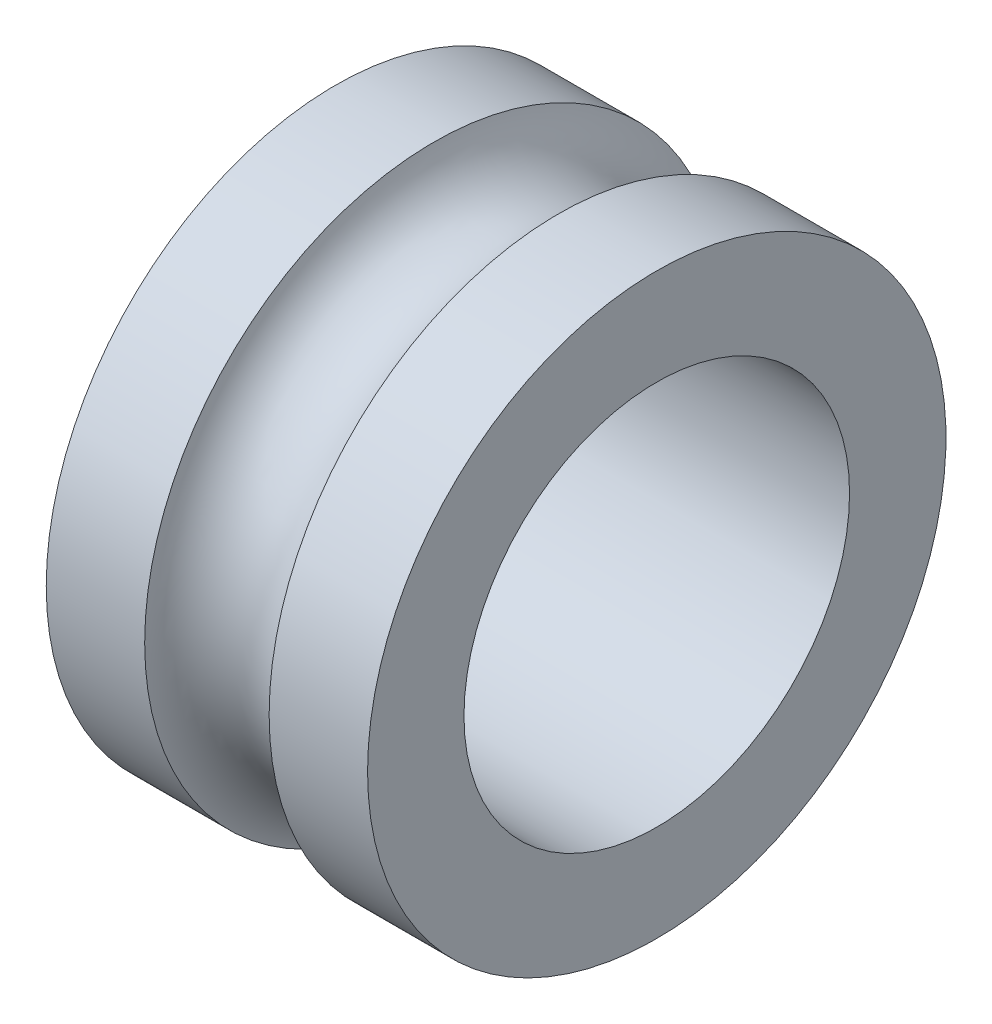
SolidWorks part; units mm, degrees
material "Stainless Steel (ferritic)"
ref_plane "Front Plane" through (0, 0, 0) normal (0, 0, 1) x (1, 0, 0)
ref_plane "Top Plane" through (0, 0, 0) normal (0, 1, 0) x (1, 0, 0)
ref_plane "Right Plane" through (0, 0, 0) normal (1, 0, 0) x (0, 0, -1)
sketch "Sketch1" plane through (0, 0, 0) normal (0, 0, 1) x (1, 0, 0)
  line L0 (-27.4435, -5.7926) -> (-27.4435, -11.7926) construction
  line L1 (-24.9435, -4.2926) -> (-26.4752, -4.2926)
  line L2 (-29.9435, -4.2926) -> (-29.9435, -5.7926)
  line L3 (-29.9435, -5.7926) -> (-24.9435, -5.7926)
  line L4 (-24.9435, -4.2926) -> (-24.9435, -5.7926)
  line L5 (-27.4435, -8.7926) -> (-26.4435, -8.7926) construction
  line L7 (-28.4117, -4.2926) -> (-29.9435, -4.2926)
  arc A0 (-28.4117, -4.2926) -> (-26.4752, -4.2926) centre (-27.4435, -4.0426) ccw
revolve "Revolve1" add sketch "Sketch1" angle 360 about L5
